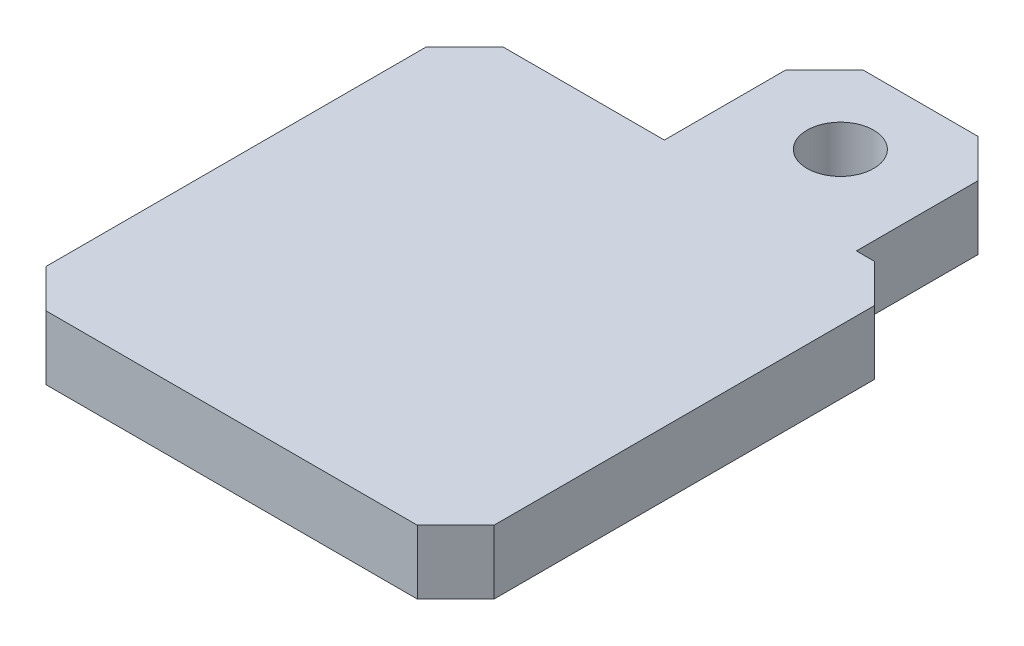
SolidWorks part; units mm, degrees
ref_plane "Front Plane" through (0, 0, 0) normal (0, 0, 1) x (1, 0, 0)
ref_plane "Top Plane" through (0, 0, 0) normal (0, 1, 0) x (1, 0, 0)
ref_plane "Right Plane" through (0, 0, 0) normal (1, 0, 0) x (0, 0, -1)
sketch "Sketch1" plane through (0, 0, 0) normal (0, 1, 0) x (1, 0, 0)
  line L0 (0, 17.5) -> (0, 30) construction
  line L1 (-17.5, -17.5) -> (17.5, -17.5)
  line L2 (-17.5, -17.5) -> (-17.5, 17.5)
  line L3 (-17.5, 17.5) -> (17.5, 17.5)
  line L4 (17.5, -17.5) -> (17.5, 17.5)
  line L5 (-17.5, -17.5) -> (17.5, 17.5) construction
  line L6 (-17.5, 17.5) -> (17.5, -17.5) construction
  line L7 (7.5, 17.5) -> (-7.5, 17.5) construction
  line L8 (-7.5, 17.5) -> (-7.5, 30) construction
  line L9 (7.5, 17.5) -> (7.5, 30)
  line L10 (7.5, 30) -> (-1.9, 30)
  line L11 (7.5, 17.5) -> (13.1, 17.5) construction
  line L12 (13.1, 17.5) -> (13.1, 30)
  line L13 (13.1, 30) -> (7.5, 30)
  line L14 (-7.5, 17.5) -> (-1.9, 17.5) construction
  line L15 (-1.9, 17.5) -> (-1.9, 30)
  line L16 (13.1, 23.75) -> (-1.9, 23.75) construction
  line L17 (-17.5, -17.5) -> (-17.5, -18.2)
  line L18 (-17.5, -18.2) -> (17.5, -18.2)
  line L19 (17.5, -18.2) -> (17.5, -17.5)
  circle A1 centre (0, 23.75) radius 2.5 construction
  circle A2 centre (5.6, 23.75) radius 2.6
  point P0 (0, 0)
  point P11 (0, 17.5)
  dimension "D3" = 5
  dimension "D7" = 5.2
  dimension "D1" = 35
  dimension "D2" = 12.5
  dimension "D4" = 7.5
  dimension "D5" = 5.6
  dimension "D6" = 5.6
  dimension "D8" = 0.7
extrude "Boss-Extrude1" add sketch "Sketch1" along normal blind 5 contours A2 L9 L3 L12 L13 | A2 L9 L10 L15 L3 | L18 L19 L1 L17 | L1 L4 L3 L2
chamfer "Chamfer1" distance 3 angle 45 6 edges at (13.1, 2.5, -30) (-1.9, 2.5, -30) (17.5, 2.5, 18.2) (17.5, 2.5, -17.5) (-17.5, 2.5, 18.2) (-17.5, 2.5, -17.5)
ref_plane "Plane2" through (0, 0.3, 0) normal (0, 1, 0) x (1, 0, 0)
sketch "Sketch4" plane through (0, 0.3, 0) normal (0, 1, 0) x (1, 0, 0)
  circle A0 centre (5.6, 23.75) radius 2.6
  circle A1 centre (5.6, 23.75) radius 1.58
  dimension "D1" = 5.2
  dimension "D2" = 3.16
extrude "Boss-Extrude2" add sketch "Sketch4" along normal blind 1
